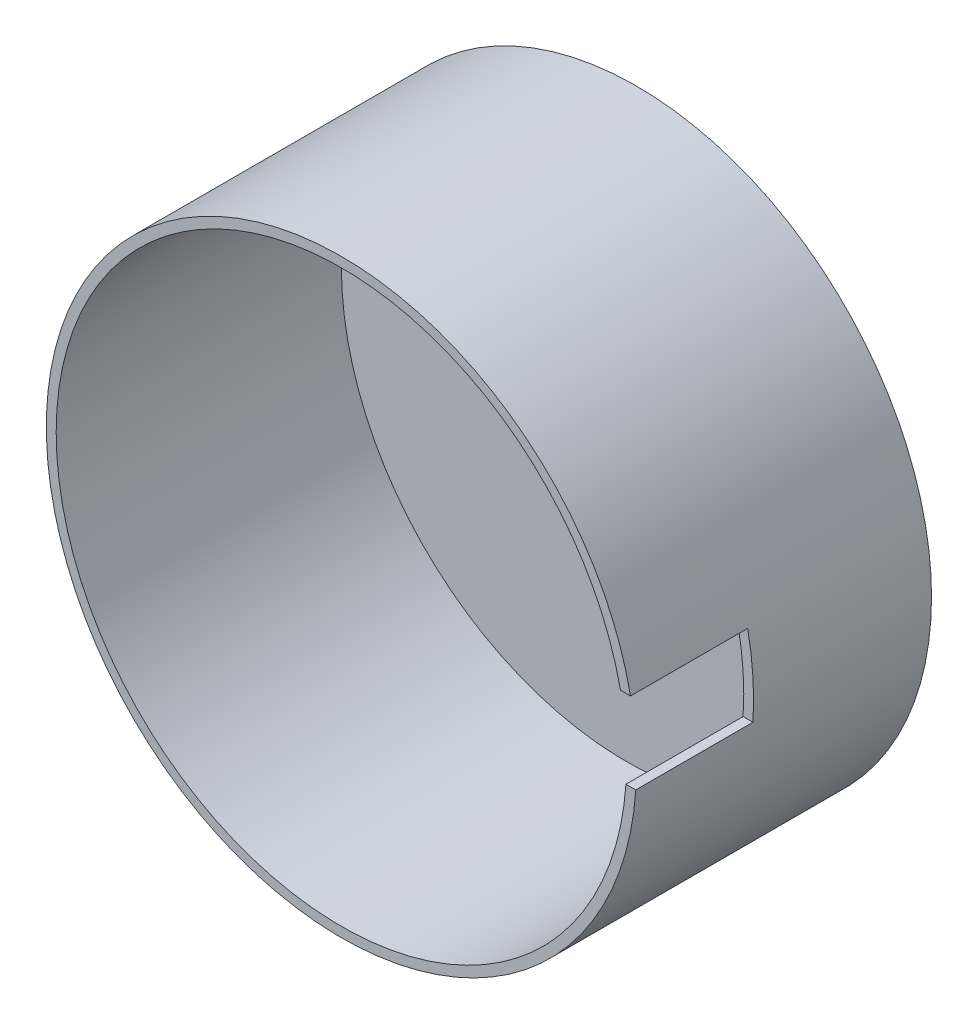
SolidWorks part; units mm, degrees
ref_plane "Front Plane" through (0, 0, 0) normal (0, 0, 1) x (1, 0, 0)
ref_plane "Top Plane" through (0, 0, 0) normal (0, 1, 0) x (1, 0, 0)
ref_plane "Right Plane" through (0, 0, 0) normal (1, 0, 0) x (0, 0, -1)
sketch "Sketch1" plane through (0, 0, 0) normal (0, 0, 1) x (1, 0, 0)
  circle A0 centre (0, 0) radius 150
  dimension "D1" = 300
extrude "Boss-Extrude1" add sketch "Sketch1" along normal blind 150
shell "Shell2" thickness 5
sketch "Sketch4" plane through (0, 0, 0) normal (1, 0, 0) x (0, 0, -1)
  line L1 (-150.4452, 29.9406) -> (-90.4452, 29.9406)
  line L2 (-150.4452, 29.9406) -> (-150.4452, -10.0594)
  line L3 (-150.4452, -10.0594) -> (-90.4452, -10.0594)
  line L4 (-90.4452, 29.9406) -> (-90.4452, -10.0594)
  line L5 (-150.4452, 29.9406) -> (-90.4452, -10.0594) construction
  line L6 (-150.4452, -10.0594) -> (-90.4452, 29.9406) construction
  point P0 (-120.4452, 9.9406)
extrude "Cut-Extrude1" cut sketch "Sketch4" along normal blind 150
